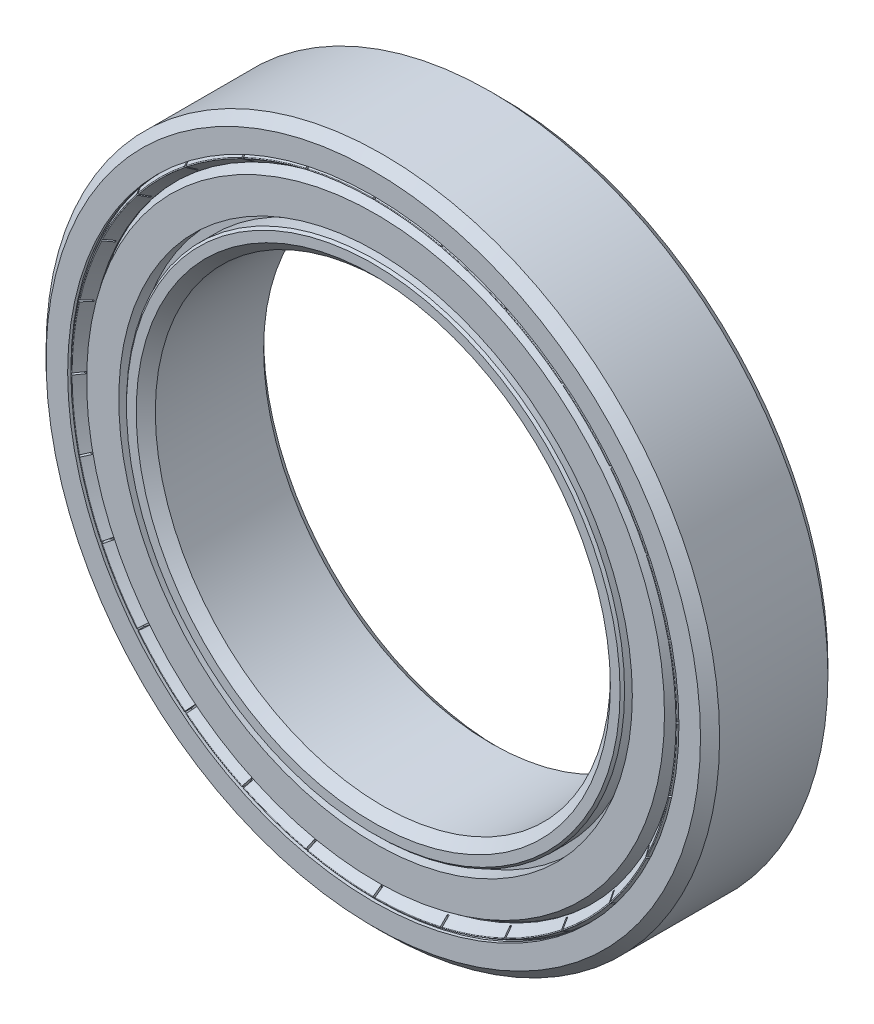
SolidWorks part; units mm, degrees
material "Alloy Steel"
ref_plane "Front Plane" through (0, 0, 0) normal (0, 0, 1) x (1, 0, 0)
ref_plane "Top Plane" through (0, 0, 0) normal (0, 1, 0) x (1, 0, 0)
ref_plane "Right Plane" through (0, 0, 0) normal (1, 0, 0) x (0, 0, -1)
sketch "Sketch1" plane through (0, 0, 0) normal (0, 0, 1) x (1, 0, 0)
  circle A0 centre (0, 0) radius 12.5
  circle A1 centre (0, 0) radius 18.5
  dimension "OD" = 37
  dimension "ID" = 25
sketch "Sketch2" plane through (0, 0, 0) normal (1, 0, 0) x (0, 0, -1)
  line L0 (-3.5, 18.5) -> (3.5, 18.5)
  line L1 (-3.5, 12.5) -> (-3.5, -12.5) construction
  line L2 (3.5, 18.5) -> (3.5, -18.5) construction
  line L3 (-3.5, 0) -> (3.5, 0) construction
  line L6 (0, 18.5) -> (0, 12.5) construction
  circle A0 centre (0, 15.5) radius 2.1 construction
  point P8 (0, 18.5)
  dimension "Approx. Ball Dia." = 4.2
  dimension "Width" = 7
  dimension "For Shaft Diameter" = 25
  dimension "For Housing ID" = 37
sketch "Sketch3" plane through (0, 0, 0) normal (1, 0, 0) x (0, 0, -1)
  line L0 (0, 0) -> (0, 25) construction
  line L1 (-3.5, 12.5) -> (-3.5, -12.5) construction
  line L2 (2.975, 18.5) -> (-2.975, 18.5)
  line L3 (-2.975, 18.5) -> (-3.5, 17.975)
  line L4 (-3.5, 17.975) -> (-3.5, 16.7898)
  line L5 (-3.5, 16.7898) -> (-3.325, 16.7898)
  line L6 (-3.325, 16.7898) -> (-3.325, 17.1949)
  line L7 (-3.325, 17.1949) -> (-3.2013, 17.3187)
  line L8 (-3.2013, 17.3187) -> (-1.05, 17.3187)
  line L10 (-3.5, 18.5) -> (3.5, 18.5) construction
  line L12 (-3.325, 17.1949) -> (-3.325, 17.6) construction
  line L13 (3.2013, 17.3187) -> (1.05, 17.3187)
  line L14 (3.325, 17.1949) -> (3.2013, 17.3187)
  line L15 (3.325, 16.7898) -> (3.325, 17.1949)
  line L16 (3.5, 16.7898) -> (3.325, 16.7898)
  line L17 (3.5, 17.975) -> (3.5, 16.7898)
  line L18 (2.975, 18.5) -> (3.5, 17.975)
  line L19 (2.975, 12.5) -> (-2.975, 12.5)
  line L20 (-2.975, 12.5) -> (-3.5, 13.025)
  line L21 (-3.5, 13.025) -> (-3.5, 13.5576)
  line L22 (-3.5, 13.5576) -> (-3.3763, 13.6813)
  line L23 (-3.3763, 13.6813) -> (-1.05, 13.6813)
  line L25 (3.3763, 13.6813) -> (1.05, 13.6813)
  line L26 (3.5, 13.5576) -> (3.3763, 13.6813)
  line L27 (3.5, 13.025) -> (3.5, 13.5576)
  line L28 (2.975, 12.5) -> (3.5, 13.025)
  circle A2 centre (0, 15.5) radius 2.1 construction
  arc A3 (-1.05, 17.3187) -> (1.05, 17.3187) centre (0, 15.5) cw
  arc A4 (-1.05, 13.6813) -> (1.05, 13.6813) centre (0, 15.5) ccw
  point P5 (0, 17.6)
  point P31 (0, 18.5)
  point P37 (0, 12.5)
  dimension "D1" = 45
  dimension "D2" = 0.175
  dimension "D3" = 2.1
  dimension "D4" = 0.525
revolve "Revolve1" add sketch "Sketch3" angle 360 about L3
sketch "Sketch4" plane through (0, 0, 0) normal (1, 0, 0) x (0, 0, -1)
  line L0 (0, 17.6) -> (0, 13.4)
  line L1 (0, 18.5) -> (0, 12.5) construction
  circle A0 centre (0, 15.5) radius 2.1 construction
  arc A1 (0, 13.4) -> (0, 17.6) centre (0, 15.5) cw
revolve "Revolve2" add sketch "Sketch4" angle 360 about L6
pattern_circular "CirPattern1" count 14 over 360 about axis through (0, 0, 0) along (0, 0, 1) of bodies 106
sketch "Sketch5" plane through (0, 0, 0) normal (1, 0, 0) x (0, 0, -1)
  line L0 (-2.1, 15.5) -> (-2.1, 13.6813) construction
  line L1 (-3.3763, 13.6813) -> (-1.05, 13.6813) construction
  line L3 (-2.1, 13.6813) -> (-2.5254, 13.6813)
  line L4 (-2.5254, 13.6813) -> (-2.5254, 14.1068)
  line L5 (-2.5254, 14.1068) -> (-3.3763, 14.1068)
  line L6 (-3.3763, 14.1068) -> (-3.3763, 15.8732)
  line L7 (-3.3763, 15.8732) -> (-2.5254, 16.3644)
  line L8 (-2.5254, 16.3644) -> (-2.1, 16.3644)
  line L9 (-2.1, 16.3644) -> (-2.1, 13.6813)
  line L10 (0, 15.5) -> (0, 18.5) construction
  line L11 (2.5254, 16.3644) -> (2.1, 16.3644)
  line L12 (3.3763, 15.8732) -> (2.5254, 16.3644)
  line L13 (3.3763, 14.1068) -> (3.3763, 15.8732)
  line L14 (2.5254, 14.1068) -> (3.3763, 14.1068)
  line L15 (2.5254, 13.6813) -> (2.5254, 14.1068)
  line L16 (2.1, 13.6813) -> (2.5254, 13.6813)
  line L17 (2.1, 16.3644) -> (2.1, 13.6813)
  line L18 (-3.3763, 15.8732) -> (-2.9508, 15.8732) construction
  line L19 (-2.9508, 15.8732) -> (-2.5254, 15.8732) construction
  line L20 (-2.5254, 15.8732) -> (-2.1, 15.8732) construction
  line L21 (-2.5254, 16.3644) -> (-2.5254, 16.7898) construction
  circle A0 centre (0, 15.5) radius 2.1 construction
  dimension "D1" = 30
revolve "Revolve3" add sketch "Sketch5" angle 360 about L3
sketch "Sketch6" plane through (0, 0, 0) normal (1, 0, 0) x (0, 0, -1)
  line L0 (-2.7978, 16.7898) -> (-3.1937, 16.7898)
  line L1 (-3.1937, 16.7898) -> (-3.5, 16.613)
  line L2 (-3.5, 16.613) -> (-2.9028, 16.1948)
  line L4 (-3.3763, 15.8732) -> (-2.5254, 16.3644) construction
  line L5 (-2.7978, 16.2072) -> (-2.7978, 16.7898)
  line L6 (-3.5, 16.7898) -> (-3.325, 16.7898) construction
  line L7 (-2.9028, 16.1948) -> (-2.8678, 16.1948)
  line L8 (-2.8678, 16.1948) -> (-2.7978, 16.2072)
  line L9 (-3.5, 17.975) -> (-3.5, -17.975) construction
  line L11 (-2.8678, 16.1948) -> (-2.8328, 16.1948) construction
  line L12 (-2.8328, 16.1948) -> (-2.7978, 16.1948) construction
  point P27 (-2.9958, 16.7898)
  dimension "D1" = 30
  dimension "D3" = 10
  dimension "D2" = 35
  dimension "D4" = 0.035
  dimension "D5" = 0.3062
revolve "Revolve4" add sketch "Sketch6" angle 360 about L3
fillet "Fillet1" radius 0.035 1 edges at (16.613, 0, 3.5)
sketch "Sketch7" plane through (0, 0, 0) normal (0, 0, 1) x (1, 0, 0)
  line L0 (-0.05, 16.7898) -> (-0.05, 16.8898)
  line L1 (-0.05, 16.7898) -> (0.05, 16.7898) construction
  line L2 (-0.05, 16.7898) -> (-0.05, 16.1948)
  line L3 (-0.05, 16.1948) -> (0.05, 16.1948) construction
  line L4 (0.05, 16.7898) -> (0.05, 16.1948)
  line L5 (-0.05, 16.8898) -> (0.05, 16.8898)
  line L6 (0.05, 16.8898) -> (0.05, 16.7898)
  line L7 (-0.05, 16.1948) -> (-0.05, 16.0948)
  line L8 (-0.05, 16.0948) -> (0.05, 16.0948)
  line L9 (0.05, 16.0948) -> (0.05, 16.1948)
  dimension "D1" = 0.1
extrude "Cut-Extrude1" cut sketch "Sketch7" along normal through all from vertex at 2.9958 starting at point (0, 16.7898, 2.9958)
pattern_circular "CirPattern2" count 28 over 360 about axis through (0, 0, 0) along (0, 0, 1) of "Cut-Extrude1"
mirror "Mirror1" about plane through (0, 0, 0) normal (0, 0, 1) of bodies 120
equation "\"Approx. Ball Dia.@Sketch2\"=( \"OD@Sketch1\" - \"ID@Sketch1\" )  * .5 * .7"
equation "\"D2@Sketch3\"=\"Width@Sketch2\"*.025"
equation "\"D3@Sketch3\"=\"Approx. Ball Dia.@Sketch2\"*.5"
equation "\"D4@Sketch3\"=\"Width@Sketch2\"*.075"
equation "\"Approx No of Balls\"= ( pi * \"OD@Sketch1\" ) * .5 / \"Approx. Ball Dia.@Sketch2\""
equation "\"D1@CirPattern1\"=\"Approx No of Balls\""
equation "\"D4@Sketch6\"=\"D2@Sketch3\"*.2"
equation "\"D1@CirPattern2\"=\"Approx No of Balls\"*2"
equation "\"D5@Sketch6\"=\"D2@Sketch3\"*1.75"
equation "\"D1@Fillet1\"=\"d4@sketch6\""
